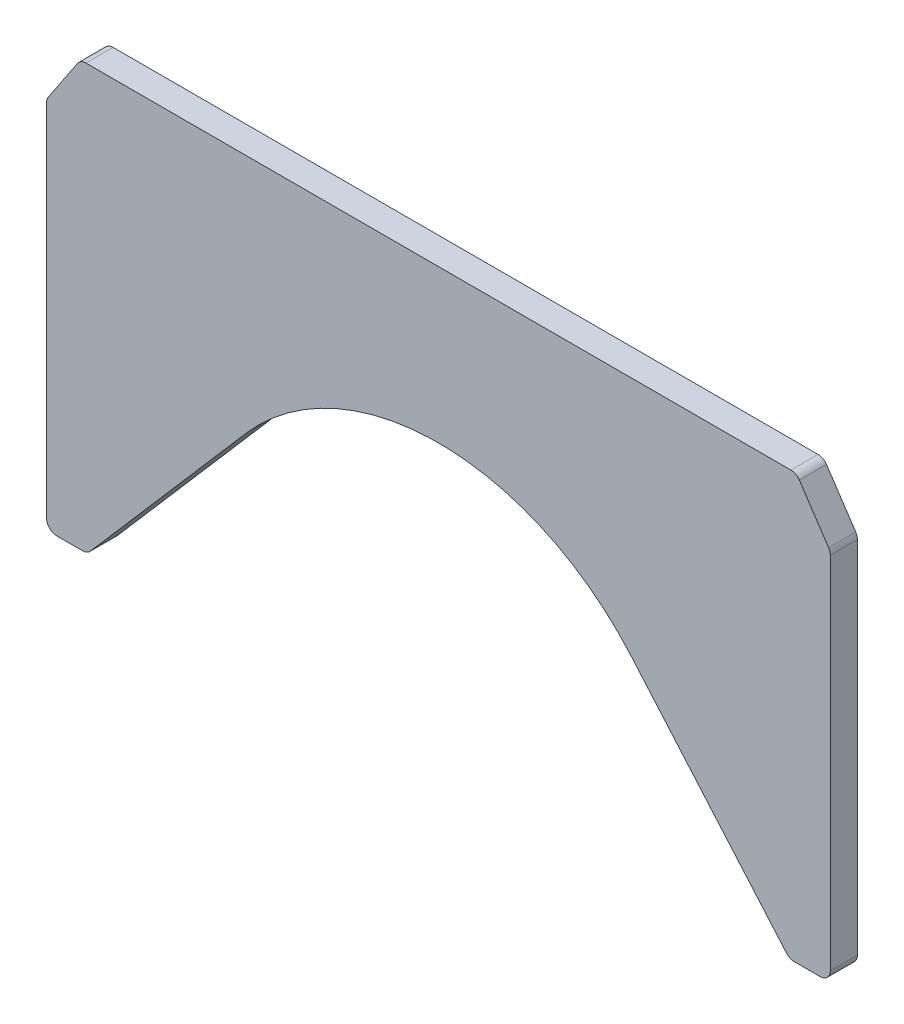
SolidWorks part; units mm, degrees
ref_plane "Plane1" through (0, 0, 0) normal (0, 0, 1) x (1, 0, 0)
ref_plane "Plane2" through (0, 0, 0) normal (0, 1, 0) x (1, 0, 0)
ref_plane "Plane3" through (0, 0, 0) normal (1, 0, 0) x (0, 0, -1)
sketch "Sketch1" plane through (0, 0, 0) normal (0, 0, 1) x (1, 0, 0)
  line L0 (-103.8944, 0) -> (103.8944, 0)
  line L1 (106.3906, -1.3359) -> (114.9962, -14.2442)
  line L2 (115.5, -15.9083) -> (115.5, -122)
  line L3 (112.5, -125) -> (104.8714, -125)
  line L4 (102.6027, -123.9629) -> (56.7184, -70.9284)
  line L5 (0, 0) -> (0, -104) construction
  line L6 (-102.6027, -123.9629) -> (-56.7184, -70.9284)
  line L7 (-112.5, -125) -> (-104.8714, -125)
  line L8 (-115.5, -15.9083) -> (-115.5, -122)
  line L9 (-106.3906, -1.3359) -> (-114.9962, -14.2442)
  arc A0 (56.7184, -70.9284) -> (-56.7184, -70.9284) centre (0, -120) ccw
  arc A1 (115.5, -122) -> (112.5, -125) centre (112.5, -122) cw
  arc A2 (104.8714, -125) -> (102.6027, -123.9629) centre (104.8714, -122) cw
  arc A3 (-102.6027, -123.9629) -> (-104.8714, -125) centre (-104.8714, -122) cw
  arc A4 (-112.5, -125) -> (-115.5, -122) centre (-112.5, -122) cw
  arc A5 (-115.5, -15.9083) -> (-114.9962, -14.2442) centre (-112.5, -15.9083) cw
  arc A6 (-106.3906, -1.3359) -> (-103.8944, 0) centre (-103.8944, -3) cw
  arc A7 (103.8944, 0) -> (106.3906, -1.3359) centre (103.8944, -3) cw
  arc A8 (114.9962, -14.2442) -> (115.5, -15.9083) centre (112.5, -15.9083) cw
  point P16 (115.5, -125)
  point P19 (103.5, -125)
  point P22 (-103.5, -125)
  point P25 (-115.5, -125)
  point P28 (-115.5, -15)
  point P31 (-105.5, 0)
  point P34 (105.5, 0)
  point P37 (115.5, -15)
  dimension "D1" = 75
  dimension "D7" = 45
  dimension "D8" = 3
  dimension "D2" = 231
  dimension "D3" = 10
  dimension "D4" = 15
  dimension "D5" = 12
  dimension "D6" = 125
extrude "Extrude1" add sketch "Sketch1" along normal blind 8
